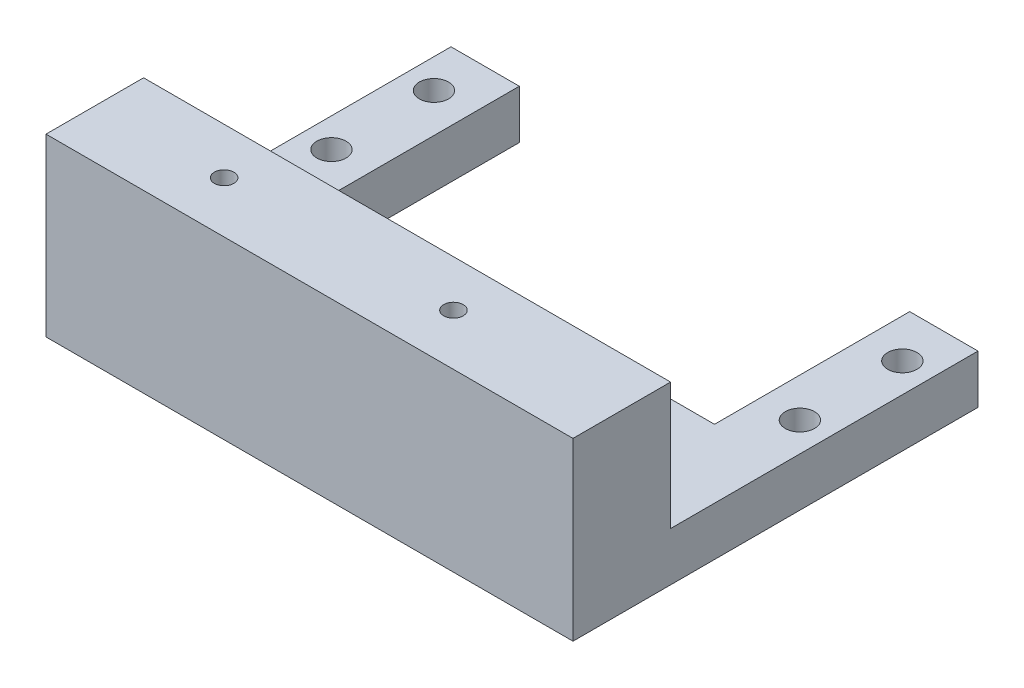
SolidWorks part; units mm, degrees
ref_plane "Front Plane" through (0, 0, 0) normal (0, 0, 1) x (1, 0, 0)
ref_plane "Top Plane" through (0, 0, 0) normal (0, 1, 0) x (1, 0, 0)
ref_plane "Right Plane" through (0, 0, 0) normal (1, 0, 0) x (0, 0, -1)
sketch "Sketch1" plane through (0, 0, 0) normal (0, 1, 0) x (1, 0, 0)
  line L0 (-20, 20.75) -> (-20, 0.75)
  line L1 (27, -20.75) -> (-27, -20.75)
  line L2 (27, -20.75) -> (27, 20.75)
  line L3 (27, 20.75) -> (20, 20.75)
  line L4 (-27, -20.75) -> (-27, 20.75)
  line L7 (-20, 0.75) -> (20, 0.75)
  line L8 (20, 0.75) -> (20, 20.75)
  line L9 (20, 20.75) -> (27, 20.75)
  line L10 (-20, 20.75) -> (-27, 20.75)
  line L11 (-20, 20.75) -> (-27, 20.75)
  point P0 (0, 0)
  dimension "D1" = 54
  dimension "D2" = 41.5
  dimension "D3" = 7
  dimension "D4" = 7
  dimension "D5" = 20
extrude "Boss-Extrude1" add sketch "Sketch1" along normal blind 5 contours L0 L10 L4 L1 L2 L3 L8 L7
sketch "Sketch2" plane through (0, 5, 0) normal (0, 1, 0) x (1, 0, 0)
  line L0 (27, 20.75) -> (20, 20.75) construction
  line L1 (20, 0.75) -> (20, 20.75) construction
  line L2 (-20, 20.75) -> (-27, 20.75) construction
  line L3 (-20, 20.75) -> (-20, 0.75) construction
  circle A0 centre (-24, 16) radius 1.5
  circle A1 centre (-24, 5.5) radius 1.5
  circle A2 centre (24, 16) radius 1.5
  circle A3 centre (24, 5.5) radius 1.5
  dimension "D1" = 3
  dimension "D2" = 3
  dimension "D3" = 3
  dimension "D4" = 3
  dimension "D5" = 4.75
  dimension "D6" = 10.5
  dimension "D7" = 4.75
  dimension "D8" = 4
  dimension "D9" = 10.5
  dimension "D10" = 4.75
  dimension "D11" = 4
extrude "Cut-Extrude1" cut sketch "Sketch2" against normal through all
sketch "Sketch3" plane through (0, 5, 0) normal (0, 1, 0) x (1, 0, 0)
  line L0 (27, -20.75) -> (27, 20.75) construction
  line L1 (-27, -20.75) -> (27, -20.75)
  line L2 (-27, -20.75) -> (-27, -10.75)
  line L3 (-27, -10.75) -> (27, -10.75)
  line L4 (27, -20.75) -> (27, -10.75)
  dimension "D1" = 10
extrude "Boss-Extrude2" add sketch "Sketch3" along normal blind 13
sketch "Sketch4" plane through (0, 18, 0) normal (0, 1, 0) x (1, 0, 0)
  line L0 (27, -20.75) -> (27, -10.75) construction
  line L1 (-27, -10.75) -> (-27, -20.75) construction
  line L2 (-27, -20.75) -> (27, -20.75) construction
  circle A0 centre (-14, -15.5) radius 1
  circle A1 centre (9.5, -15.5) radius 1
  dimension "D1" = 2
  dimension "D2" = 2
  dimension "D3" = 17.5
  dimension "D4" = 13
  dimension "D5" = 5.25
  dimension "D6" = 5.25
extrude "Cut-Extrude2" cut sketch "Sketch4" against normal blind 6
